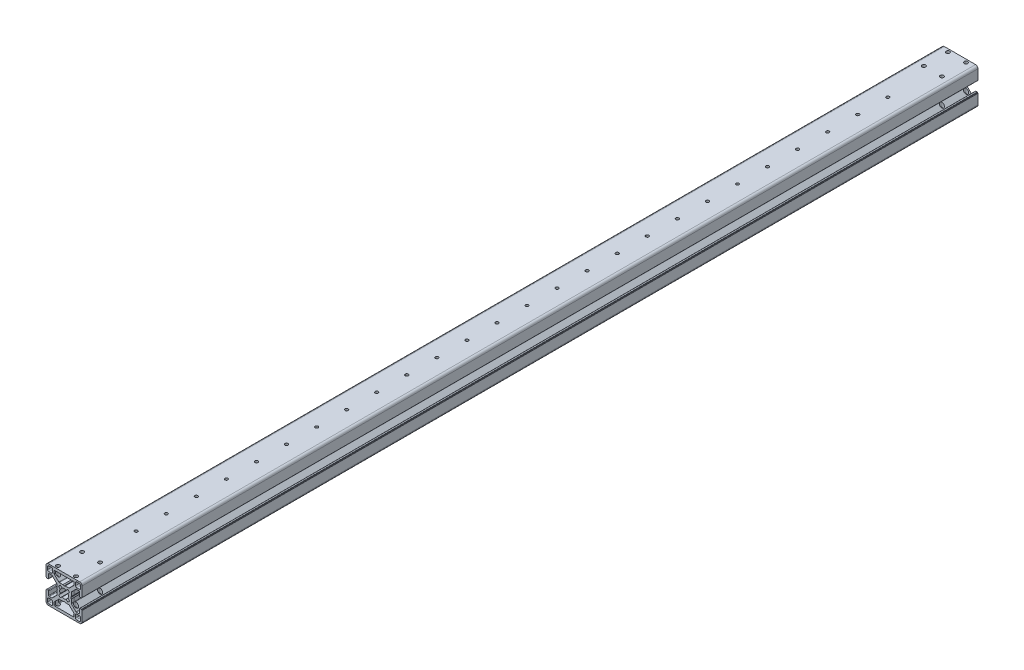
SolidWorks part; units mm, degrees
ref_plane "Ebene vorne" through (0, 0, 0) normal (0, 0, 1) x (1, 0, 0)
ref_plane "Ebene oben" through (0, 0, 0) normal (0, 1, 0) x (1, 0, 0)
ref_plane "Ebene rechts" through (0, 0, 0) normal (1, 0, 0) x (0, 0, -1)
ref_plane "Ebene1" through (0, 0, 1000) normal (0, 0, 1) x (1, 0, 0)
sketch "Skizze1" plane through (0, 0, 1000) normal (0, 0, 1) x (1, 0, 0)
  line L0 (2.5, -5.5) -> (0.3, -5.5)
  line L1 (-0.7, -4.5) -> (-0.7, -2.3)
  line L2 (0.3, -1.3) -> (2.5, -1.3)
  line L3 (3.5, -2.3) -> (3.5, -4.5)
  line L4 (3.5, -25.5) -> (3.5, -27.7)
  line L5 (2.5, -28.7) -> (0.3, -28.7)
  line L6 (-0.7, -27.7) -> (-0.7, -25.5)
  line L7 (0.3, -24.5) -> (2.5, -24.5)
  line L8 (23.5, -24.5) -> (25.7, -24.5)
  line L9 (26.7, -25.5) -> (26.7, -27.7)
  line L10 (25.7, -28.7) -> (23.5, -28.7)
  line L11 (22.5, -27.7) -> (22.5, -25.5)
  line L12 (22.5, -4.5) -> (22.5, -2.3)
  line L13 (23.5, -1.3) -> (25.7, -1.3)
  line L14 (26.7, -2.3) -> (26.7, -4.5)
  line L15 (25.7, -5.5) -> (23.5, -5.5)
  line L16 (16.1359, -19.5184) -> (14.6001, -18.2806)
  line L17 (11.3999, -18.2806) -> (9.8641, -19.5184)
  line L18 (8.4947, -18.1547) -> (9.7194, -16.6001)
  line L19 (9.7194, -13.3999) -> (8.4947, -11.8453)
  line L20 (9.8641, -10.4816) -> (11.3999, -11.7194)
  line L21 (14.6001, -11.7194) -> (16.1359, -10.4816)
  line L22 (17.5053, -11.8453) -> (16.2806, -13.3999)
  line L23 (16.2806, -16.6001) -> (17.5053, -18.1547)
  line L24 (17.3509, -21.1466) -> (21.1037, -24.9036)
  line L25 (21.25, -25.2569) -> (21.25, -27.3)
  line L26 (20.75, -27.8) -> (5.25, -27.8)
  line L27 (4.75, -27.3) -> (4.75, -25.2569)
  line L28 (4.8963, -24.9036) -> (8.6491, -21.1466)
  line L29 (9.0028, -21) -> (12.0468, -21)
  line L30 (12.1462, -20.9736) -> (12.9006, -20.5417)
  line L31 (13.0994, -20.5417) -> (13.8538, -20.9736)
  line L32 (13.9532, -21) -> (16.9972, -21)
  line L33 (16.9972, -9) -> (13.9532, -9)
  line L34 (13.8538, -9.0264) -> (13.0994, -9.4583)
  line L35 (12.9006, -9.4583) -> (12.1462, -9.0264)
  line L36 (12.0468, -9) -> (9.0028, -9)
  line L37 (8.6491, -8.8534) -> (4.8963, -5.0964)
  line L38 (4.75, -4.7431) -> (4.75, -2.7)
  line L39 (5.25, -2.2) -> (20.75, -2.2)
  line L40 (21.25, -2.7) -> (21.25, -4.7431)
  line L41 (21.1037, -5.0964) -> (17.3509, -8.8534)
  line L42 (0, -30) -> (26, -30)
  line L43 (28, -28) -> (28, -19.7)
  line L44 (27.8, -19.5) -> (27.5, -19.5)
  line L45 (27.5, -19.5) -> (27.5, -19.2)
  line L46 (27.3, -19) -> (26.3, -19)
  line L47 (25.8, -19.5) -> (25.8, -22.75)
  line L48 (25.3, -23.25) -> (23.2571, -23.25)
  line L49 (22.9036, -23.1036) -> (19.1509, -19.3509)
  line L50 (19.0045, -18.9974) -> (19.0045, -15.9536)
  line L51 (18.9777, -15.8536) -> (18.5426, -15.1)
  line L52 (18.5426, -14.9) -> (18.9777, -14.1464)
  line L53 (19.0045, -14.0464) -> (19.0045, -11.0026)
  line L54 (19.1509, -10.6491) -> (22.9036, -6.8964)
  line L55 (23.2571, -6.75) -> (25.3, -6.75)
  line L56 (25.8, -7.25) -> (25.8, -10.5)
  line L57 (26.3, -11) -> (27.3, -11)
  line L58 (27.5, -10.8) -> (27.5, -10.5)
  line L59 (27.5, -10.5) -> (27.8, -10.5)
  line L60 (28, -10.3) -> (28, -2)
  line L61 (26, 0) -> (0, 0)
  line L62 (-2, -2) -> (-2, -10.3)
  line L63 (-1.8, -10.5) -> (-1.5, -10.5)
  line L64 (-1.5, -10.5) -> (-1.5, -10.8)
  line L65 (-1.3, -11) -> (-0.3, -11)
  line L66 (0.2, -10.5) -> (0.2, -7.25)
  line L67 (0.7, -6.75) -> (2.7429, -6.75)
  line L68 (3.0964, -6.8964) -> (6.8491, -10.6491)
  line L69 (6.9955, -11.0026) -> (6.9955, -14.0464)
  line L70 (7.0223, -14.1464) -> (7.4574, -14.9)
  line L71 (7.4574, -15.1) -> (7.0223, -15.8536)
  line L72 (6.9955, -15.9536) -> (6.9955, -18.9974)
  line L73 (6.8491, -19.3509) -> (3.0964, -23.1036)
  line L74 (2.7429, -23.25) -> (0.7, -23.25)
  line L75 (0.2, -22.75) -> (0.2, -19.5)
  line L76 (-0.3, -19) -> (-1.3, -19)
  line L77 (-1.5, -19.2) -> (-1.5, -19.5)
  line L78 (-1.5, -19.5) -> (-1.8, -19.5)
  line L79 (-2, -19.7) -> (-2, -28)
  arc A0 (3.5, -4.5) -> (2.5, -5.5) centre (2.5, -4.5) cw
  arc A1 (0.3, -5.5) -> (-0.7, -4.5) centre (0.3, -4.5) cw
  arc A2 (-0.7, -2.3) -> (0.3, -1.3) centre (0.3, -2.3) cw
  arc A3 (2.5, -1.3) -> (3.5, -2.3) centre (2.5, -2.3) cw
  arc A4 (2.5, -24.5) -> (3.5, -25.5) centre (2.5, -25.5) cw
  arc A5 (3.5, -27.7) -> (2.5, -28.7) centre (2.5, -27.7) cw
  arc A6 (0.3, -28.7) -> (-0.7, -27.7) centre (0.3, -27.7) cw
  arc A7 (-0.7, -25.5) -> (0.3, -24.5) centre (0.3, -25.5) cw
  arc A8 (22.5, -25.5) -> (23.5, -24.5) centre (23.5, -25.5) cw
  arc A9 (25.7, -24.5) -> (26.7, -25.5) centre (25.7, -25.5) cw
  arc A10 (26.7, -27.7) -> (25.7, -28.7) centre (25.7, -27.7) cw
  arc A11 (23.5, -28.7) -> (22.5, -27.7) centre (23.5, -27.7) cw
  arc A12 (23.5, -5.5) -> (22.5, -4.5) centre (23.5, -4.5) cw
  arc A13 (22.5, -2.3) -> (23.5, -1.3) centre (23.5, -2.3) cw
  arc A14 (25.7, -1.3) -> (26.7, -2.3) centre (25.7, -2.3) cw
  arc A15 (26.7, -4.5) -> (25.7, -5.5) centre (25.7, -4.5) cw
  arc A16 (17.5053, -18.1547) -> (16.1359, -19.5184) centre (13, -15) cw
  arc A17 (14.6001, -18.2806) -> (11.3999, -18.2806) centre (13, -15) cw
  arc A18 (9.8641, -19.5184) -> (8.4947, -18.1547) centre (13, -15) cw
  arc A19 (9.7194, -16.6001) -> (9.7194, -13.3999) centre (13, -15) cw
  arc A20 (8.4947, -11.8453) -> (9.8641, -10.4816) centre (13, -15) cw
  arc A21 (11.3999, -11.7194) -> (14.6001, -11.7194) centre (13, -15) cw
  arc A22 (16.1359, -10.4816) -> (17.5053, -11.8453) centre (13, -15) cw
  arc A23 (16.2806, -13.3999) -> (16.2806, -16.6001) centre (13, -15) cw
  arc A24 (16.9972, -21) -> (17.3509, -21.1466) centre (16.9972, -21.5) cw
  arc A25 (21.1037, -24.9036) -> (21.25, -25.2569) centre (20.75, -25.2569) cw
  arc A26 (21.25, -27.3) -> (20.75, -27.8) centre (20.75, -27.3) cw
  arc A27 (5.25, -27.8) -> (4.75, -27.3) centre (5.25, -27.3) cw
  arc A28 (4.75, -25.2569) -> (4.8963, -24.9036) centre (5.25, -25.2569) cw
  arc A29 (8.6491, -21.1466) -> (9.0028, -21) centre (9.0028, -21.5) cw
  arc A30 (12.0468, -21) -> (12.1462, -20.9736) centre (12.0468, -20.8) ccw
  arc A31 (12.9006, -20.5417) -> (13.0994, -20.5417) centre (13, -20.7153) cw
  arc A32 (13.8538, -20.9736) -> (13.9532, -21) centre (13.9532, -20.8) ccw
  arc A33 (17.3509, -8.8534) -> (16.9972, -9) centre (16.9972, -8.5) cw
  arc A34 (13.9532, -9) -> (13.8538, -9.0264) centre (13.9532, -9.2) ccw
  arc A35 (13.0994, -9.4583) -> (12.9006, -9.4583) centre (13, -9.2847) cw
  arc A36 (12.1462, -9.0264) -> (12.0468, -9) centre (12.0468, -9.2) ccw
  arc A37 (9.0028, -9) -> (8.6491, -8.8534) centre (9.0028, -8.5) cw
  arc A38 (4.8963, -5.0964) -> (4.75, -4.7431) centre (5.25, -4.7431) cw
  arc A39 (4.75, -2.7) -> (5.25, -2.2) centre (5.25, -2.7) cw
  arc A40 (20.75, -2.2) -> (21.25, -2.7) centre (20.75, -2.7) cw
  arc A41 (21.25, -4.7431) -> (21.1037, -5.0964) centre (20.75, -4.7431) cw
  arc A42 (26, -30) -> (28, -28) centre (26, -28) ccw
  arc A43 (28, -19.7) -> (27.8, -19.5) centre (27.8, -19.7) ccw
  arc A44 (27.5, -19.2) -> (27.3, -19) centre (27.3, -19.2) ccw
  arc A45 (26.3, -19) -> (25.8, -19.5) centre (26.3, -19.5) ccw
  arc A46 (25.8, -22.75) -> (25.3, -23.25) centre (25.3, -22.75) cw
  arc A47 (23.2571, -23.25) -> (22.9036, -23.1036) centre (23.2571, -22.75) cw
  arc A48 (19.1509, -19.3509) -> (19.0045, -18.9974) centre (19.5045, -18.9974) cw
  arc A49 (19.0045, -15.9536) -> (18.9777, -15.8536) centre (18.8045, -15.9536) ccw
  arc A50 (18.5426, -15.1) -> (18.5426, -14.9) centre (18.7158, -15) cw
  arc A51 (18.9777, -14.1464) -> (19.0045, -14.0464) centre (18.8045, -14.0464) ccw
  arc A52 (19.0045, -11.0026) -> (19.1509, -10.6491) centre (19.5045, -11.0026) cw
  arc A53 (22.9036, -6.8964) -> (23.2571, -6.75) centre (23.2571, -7.25) cw
  arc A54 (25.3, -6.75) -> (25.8, -7.25) centre (25.3, -7.25) cw
  arc A55 (25.8, -10.5) -> (26.3, -11) centre (26.3, -10.5) ccw
  arc A56 (27.3, -11) -> (27.5, -10.8) centre (27.3, -10.8) ccw
  arc A57 (27.8, -10.5) -> (28, -10.3) centre (27.8, -10.3) ccw
  arc A58 (28, -2) -> (26, 0) centre (26, -2) ccw
  arc A59 (0, 0) -> (-2, -2) centre (0, -2) ccw
  arc A60 (-2, -10.3) -> (-1.8, -10.5) centre (-1.8, -10.3) ccw
  arc A61 (-1.5, -10.8) -> (-1.3, -11) centre (-1.3, -10.8) ccw
  arc A62 (-0.3, -11) -> (0.2, -10.5) centre (-0.3, -10.5) ccw
  arc A63 (0.2, -7.25) -> (0.7, -6.75) centre (0.7, -7.25) cw
  arc A64 (2.7429, -6.75) -> (3.0964, -6.8964) centre (2.7429, -7.25) cw
  arc A65 (6.8491, -10.6491) -> (6.9955, -11.0026) centre (6.4955, -11.0026) cw
  arc A66 (6.9955, -14.0464) -> (7.0223, -14.1464) centre (7.1955, -14.0464) ccw
  arc A67 (7.4574, -14.9) -> (7.4574, -15.1) centre (7.2842, -15) cw
  arc A68 (7.0223, -15.8536) -> (6.9955, -15.9536) centre (7.1955, -15.9536) ccw
  arc A69 (6.9955, -18.9974) -> (6.8491, -19.3509) centre (6.4955, -18.9974) cw
  arc A70 (3.0964, -23.1036) -> (2.7429, -23.25) centre (2.7429, -22.75) cw
  arc A71 (0.7, -23.25) -> (0.2, -22.75) centre (0.7, -22.75) cw
  arc A72 (0.2, -19.5) -> (-0.3, -19) centre (-0.3, -19.5) ccw
  arc A73 (-1.3, -19) -> (-1.5, -19.2) centre (-1.3, -19.2) ccw
  arc A74 (-1.8, -19.5) -> (-2, -19.7) centre (-1.8, -19.7) ccw
  arc A75 (-2, -28) -> (0, -30) centre (0, -28) ccw
extrude "Aufsatz-Linear austragen1" add sketch "Skizze1" against normal blind 745
hole_wizard "M3 Gewindebohrung1" positions "3D-Skizze2" profile "Skizze2" tap size "M3" standard "DIN" end condition through all
sketch3d "3D-Skizze2"
  line L0 (26, 0, 1000) -> (0, 0, 1000) construction
  line L2 (0, 0, 255) -> (0, 0, 1000) construction
  line L3 (0, 0, 255) -> (26, 0, 255) construction
  point P37 (13, 0, 640)
  dimension "D1" = 360
  dimension "D2" = 13
sketch "Skizze2" plane through (13, 0, 640) normal (1, 0, 0) x (0, 0, 1)
  line L0 (0, 0) -> (0, 30)
  line L1 (0, 30) -> (1.525, 30)
  line L2 (1.25, 29.725) -> (1.25, 0)
  line L5 (1.25, 0) -> (0, 0)
  line L7 (1.525, 30) -> (1.25, 29.725)
  line L8 (-1.525, 30) -> (-1.25, 29.725) construction
  line L11 (0, -6.35) -> (0, 107.95) construction
  dimension "Bohrerdurchmesser" = 2.5
  dimension "Bohrungstiefe" = 30
  dimension "Senkdurchmesser (Unten)" = 3.05
  dimension "Senkwinkel (Unten)" = 90
cosmetic thread "Bohrungsgewinde1" parameters "D2"=3
pattern_linear "Lineares Muster1" count 14 spacing 25 along (0, 0, -1) count 13 spacing 25 along (0, 0, 1) of "M3 Gewindebohrung1"
hole_wizard "Ø3.0 (3) Durchmesser Bohrung1" positions "Skizze3" profile "Skizze4" hole size "Ø3.0" standard "DIN" end condition through all
sketch "Skizze3" plane through (0, 0, 0) normal (0, 1, 0) x (1, 0, 0)
  line L0 (0, -627.5) -> (26, -627.5) construction
  line L1 (0, -255) -> (0, -1000) construction
  line L2 (26, -255) -> (26, -1000) construction
  line L4 (13, -255) -> (13, -305.913) construction
  line L5 (26, -255) -> (0, -255) construction
  point P0 (5.5, -277.5)
  point P2 (5.5, -257.5)
  point P4 (20.5, -277.5)
  point P6 (20.5, -257.5)
  point P22 (20.5, -997.5)
  point P23 (20.5, -977.5)
  point P24 (5.5, -997.5)
  point P25 (5.5, -977.5)
  dimension "D1" = 20
  dimension "D2" = 15
  dimension "D3" = 15
  dimension "D4" = 20
  dimension "D5" = 350
  dimension "D6" = 7.5
sketch "Skizze4" plane through (5.5, 0, 277.5) normal (1, 0, 0) x (0, 0, 1)
  line L0 (0, 0) -> (0, 30)
  line L1 (0, 30) -> (1.5, 30)
  line L2 (1.5, 30) -> (1.5, 0)
  line L5 (1.5, 0) -> (0, 0)
  line L11 (0, -6.35) -> (0, 107.95) construction
  dimension "Bohrerdurchmesser" = 3
  dimension "Bohrungstiefe" = 30
